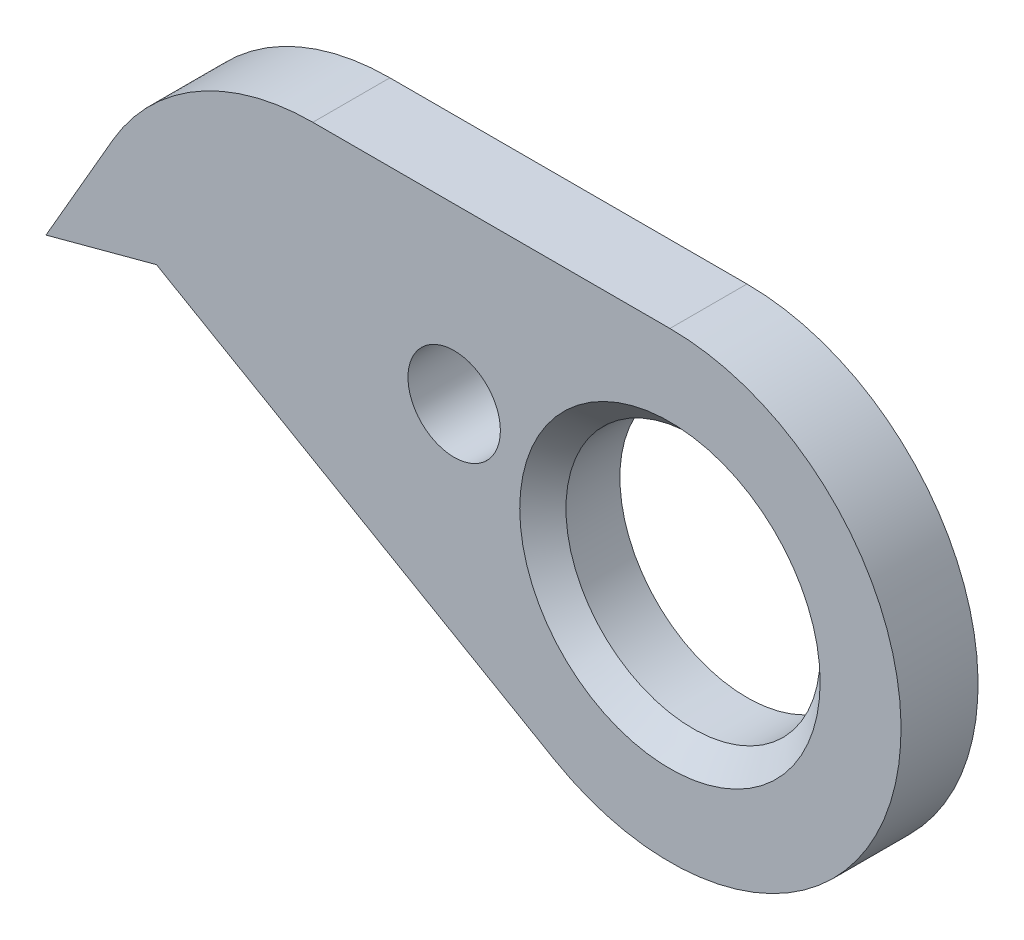
SolidWorks part; units mm, degrees
ref_plane "Front Plane" through (0, 0, 0) normal (0, 0, 1) x (1, 0, 0)
ref_plane "Top Plane" through (0, 0, 0) normal (0, 1, 0) x (1, 0, 0)
ref_plane "Right Plane" through (0, 0, 0) normal (1, 0, 0) x (0, 0, -1)
sketch "Sketch1" plane through (0, 0, 0) normal (0, 0, 1) x (1, 0, 0)
  line L0 (0, 3) -> (-4.6359, 3)
  line L1 (0, 0) -> (-8.1, 0) construction
  line L2 (-6.6657, 0.3843) -> (-1.5, -2.5981)
  line L3 (-8.1, 0) -> (-6.6657, 0.3843)
  line L4 (-8.1, 0) -> (-7.234, 1.5)
  arc A0 (-1.5, -2.5981) -> (0, 3) centre (0, 0) ccw
  arc A1 (-7.234, 1.5) -> (-4.6359, 3) centre (-4.6359, 0) cw
  dimension "D1" = 6
  dimension "D6" = 3
  dimension "D2" = 30
  dimension "D3" = 11.1
  dimension "D4" = 15
  dimension "D5" = 45
extrude "Boss-Extrude1" add sketch "Sketch1" against normal blind 1
sketch "Sketch2" plane through (0, 0, 0) normal (0, 0, 1) x (1, 0, 0)
  circle A0 centre (0, 0) radius 1.65
  dimension "D1" = 3.3
extrude "Cut-Extrude1" cut sketch "Sketch2" against normal up to next
chamfer "Chamfer1" distance 0.3 angle 45 1 edges at (1.65, 0, 0)
hole_wizard "Ø1.2 (1.2) Diameter Hole1" positions "Sketch4" profile "Sketch3" hole size "Ø1.2" standard "DIN" end condition through all
sketch "Sketch4" plane through (0, 0, 0) normal (0, 0, 1) x (1, 0, 0)
  line L0 (0, 0) -> (-2.8012, 0.7506) construction
  line L1 (0, 0) -> (-2.9, 0) construction
  circle A0 centre (0, 0) radius 2.9 construction
  point P0 (-2.8012, 0.7506)
  dimension "D1" = 15
  dimension "D2" = 5.8
sketch "Sketch3" plane through (-2.8012, 0.7506, 0) normal (1, 0, 0) x (0, -1, 0)
  line L0 (0, 0) -> (0, 1)
  line L1 (0, 1) -> (0.6, 1)
  line L2 (0.6, 1) -> (0.6, 0)
  line L5 (0.6, 0) -> (0, 0)
  line L11 (0, -6.35) -> (0, 107.95) construction
  dimension "Thru Hole Dia." = 1.2
  dimension "Thru Hole Depth" = 1
